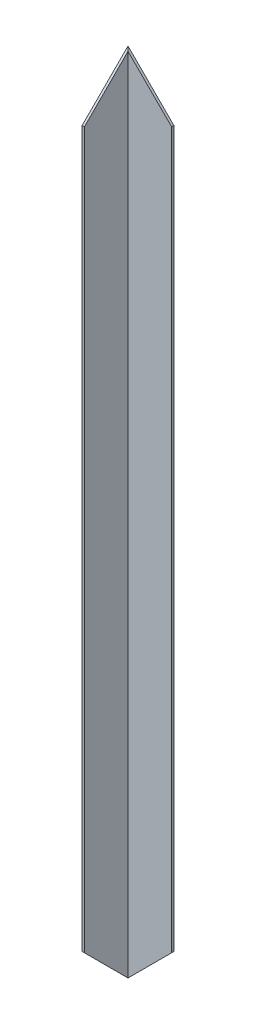
SolidWorks part; units mm, degrees
ref_plane "Plan de face" through (0, 0, 0) normal (0, 0, 1) x (1, 0, 0)
ref_plane "Plan de dessus" through (0, 0, 0) normal (0, 1, 0) x (1, 0, 0)
ref_plane "Plan de droite" through (0, 0, 0) normal (1, 0, 0) x (0, 0, -1)
sketch "Esquisse1" plane through (0, 0, 0) normal (0, 1, 0) x (1, 0, 0)
  line L1 (-20, 20.1136) -> (20, 20.1136)
  line L2 (-20, 20.1136) -> (-20, -19.8864)
  line L3 (-20, -19.8864) -> (-18, -19.8864)
  line L4 (20, 20.1136) -> (20, 18.1136)
  line L5 (-18, 18.1136) -> (20, 18.1136)
  line L6 (-18, 18.1136) -> (-18, -19.8864)
  dimension "D1" = 20
  dimension "D2" = 40
  dimension "D3" = 40
  dimension "D4" = 2
  dimension "D5" = 2
extrude "Boss.-Extru.1" add sketch "Esquisse1" along normal blind 704
sketch "Esquisse2" plane through (0, 0, -20.1136) normal (0, 0, -1) x (-1, 0, 0)
  line L0 (20, 0) -> (-20, 40)
  line L1 (20, 0) -> (-20, 0)
  line L2 (-20, 0) -> (-20, 40)
  dimension "D1" = 45
extrude "Enlèv. mat.-Extru.1" cut sketch "Esquisse2" against normal blind 590
sketch "Esquisse3" plane through (-20, 0, 0) normal (-1, 0, 0) x (0, 0, 1)
  line L0 (-20.1136, 0) -> (19.8864, 40)
  line L1 (19.8864, 704) -> (19.8864, 0) construction
  line L2 (19.8864, 40) -> (19.8864, 0)
  line L3 (19.8864, 0) -> (-20.1136, 0)
  dimension "D1" = 45
extrude "Enlèv. mat.-Extru.2" cut sketch "Esquisse3" against normal blind 590
sketch "Esquisse4" plane through (-20, 0, 0) normal (-1, 0, 0) x (0, 0, 1)
  line L0 (-20.1136, 704) -> (19.8864, 664)
  line L1 (19.8864, 704) -> (19.8864, 40) construction
  line L2 (19.8864, 664) -> (19.8864, 704)
  line L3 (19.8864, 704) -> (-20.1136, 704)
  dimension "D1" = 45
extrude "Enlèv. mat.-Extru.3" cut sketch "Esquisse4" against normal through all
sketch "Esquisse5" plane through (0, 0, -20.1136) normal (0, 0, -1) x (-1, 0, 0)
  line L0 (20, 704) -> (-20, 664)
  line L1 (-20, 704) -> (-20, 40) construction
  line L2 (-20, 664) -> (-20, 704)
  line L3 (-20, 704) -> (20, 704)
  dimension "D1" = 45
extrude "Enlèv. mat.-Extru.4" cut sketch "Esquisse5" against normal through all
